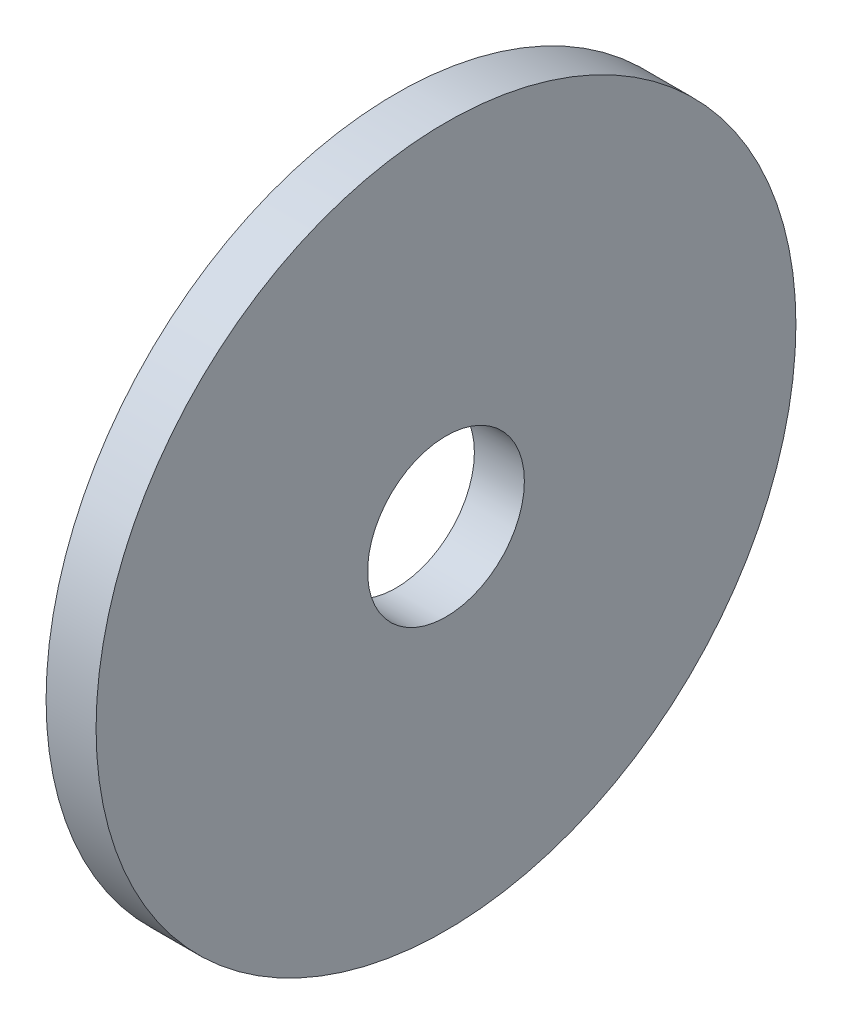
SolidWorks part; units mm, degrees
material "6061-T6 (SS)"
ref_plane "Front Plane" through (0, 0, 0) normal (0, 0, 1) x (1, 0, 0)
ref_plane "Top Plane" through (0, 0, 0) normal (0, 1, 0) x (1, 0, 0)
ref_plane "Right Plane" through (0, 0, 0) normal (1, 0, 0) x (0, 0, -1)
sketch "Sketch1" plane through (0, 0, 0) normal (1, 0, 0) x (0, 0, -1)
  circle A0 centre (0, 0) radius 11.1125
  dimension "D1" = 22.225
extrude "Boss-Extrude1" add sketch "Sketch1" along normal blind 1.5875
hole_wizard "#10 Clearance Hole1" positions "Sketch3" profile "Sketch2" hole size "#10" standard "ANSI Inch"
sketch "Sketch3" plane through (1.5875, 0, 0) normal (1, 0, 0) x (0, 0, -1)
  point P0 (0, 0)
sketch "Sketch2" plane through (1.5875, 0, 0) normal (0, 1, 0) x (0, 0, -1)
  line L0 (0, 0) -> (0, 16.4957)
  line L1 (0, 16.4957) -> (2.4892, 15)
  line L2 (2.4892, 15) -> (2.4892, 0)
  line L5 (2.4892, 0) -> (0, 0)
  line L10 (0, 16.4957) -> (-2.4892, 15) construction
  line L11 (0, -6.35) -> (0, 107.95) construction
  dimension "Hole Dia." = 4.9784
  dimension "Hole Depth" = 15
  dimension "Drill Angle" = 118
